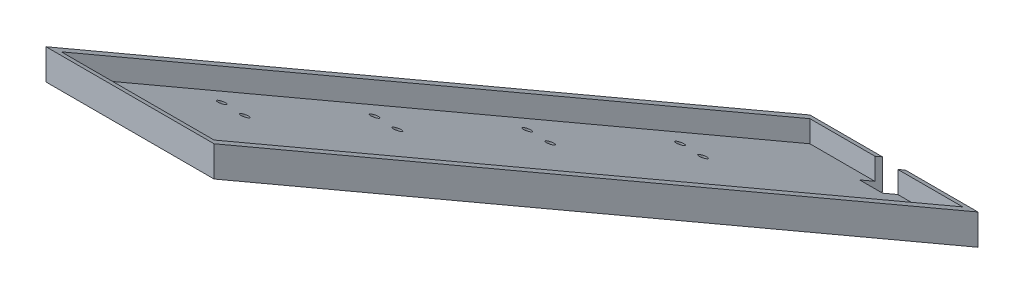
SolidWorks part; units mm, degrees
material "Acrylic (Medium-high impact)"
ref_plane "Front Plane" through (0, 0, 0) normal (0, 0, 1) x (1, 0, 0)
ref_plane "Top Plane" through (0, 0, 0) normal (0, 1, 0) x (1, 0, 0)
ref_plane "Right Plane" through (0, 0, 0) normal (1, 0, 0) x (0, 0, -1)
sketch "Sketch1" plane through (0, 0, 0) normal (1, 0, 0) x (0, 0, -1)
  line L0 (0, 20) -> (-500, 308.6751)
  line L1 (0, 20) -> (0, 0)
  line L2 (0, 0) -> (-500, 288.6751)
  line L3 (-500, 288.6751) -> (-500, 308.6751)
  line L4 (-93.7881, 0) -> (93.7881, 0) construction
  dimension "D1" = 500
  dimension "D2" = 20
  dimension "D3" = 30
extrude "Boss-Extrude1" add sketch "Sketch1" along normal blind 110
ref_plane "Plane1" through (5, 0, 0) normal (1, 0, 0) x (0, 0, -1)
sketch "Sketch3" plane through (5, 0, 0) normal (1, 0, 0) x (0, 0, -1)
  line L0 (-495, 291.5619) -> (-5, 8.6603)
  line L2 (-5, 8.6603) -> (-5, 22.8868)
  line L3 (0, 20) -> (-500, 308.6751) construction
  line L4 (-500, 288.6751) -> (0, 0) construction
  line L5 (0, 0) -> (0, 20) construction
  line L6 (-495, 291.5619) -> (-495, 305.7884)
  line L7 (-495, 305.7884) -> (-5, 22.8868)
  line L8 (-500, 308.6751) -> (-500, 288.6751) construction
  dimension "D1" = 5
  dimension "D2" = 5
  dimension "D3" = 5
extrude "Cut-Extrude1" cut sketch "Sketch3" along normal blind 100
sketch "Sketch4" plane through (0, 0, 0) normal (0, 1, 0) x (1, 0, 0)
  line L0 (110, 0) -> (0, 0) construction
  line L1 (47.5, 15) -> (62.5, 15)
  line L2 (47.5, 15) -> (47.5, -15)
  line L3 (47.5, -15) -> (62.5, -15)
  line L4 (62.5, 15) -> (62.5, -15)
  line L5 (47.5, 15) -> (62.5, -15) construction
  line L6 (47.5, -15) -> (62.5, 15) construction
  point P0 (55, 0)
  dimension "D1" = 15
  dimension "D2" = 30
extrude "Cut-Extrude2" cut sketch "Sketch4" along normal blind 90
sketch "Sketch6" plane through (0, 0, 0) normal (0, 1, 0) x (1, 0, 0)
sketch "Sketch7" plane through (0, 0, 0) normal (0, 1, 0) x (1, 0, 0)
  line L0 (20, 49.7876) -> (20, -561.1982) construction
  line L1 (90, 41.5681) -> (90, -569.4177) construction
  line L2 (55, 44.3079) -> (55, -566.6778) construction
  line L4 (5, -5) -> (5, -495) construction
  line L7 (105, -495) -> (105, -5) construction
  line L8 (-60.0832, -105) -> (204.1417, -105) construction
  line L9 (47.5, -5) -> (5, -5) construction
  circle A0 centre (20, -105) radius 2.5
  circle A1 centre (90, -105) radius 2.5
  circle A2 centre (20, -205) radius 2.5
  circle A3 centre (20, -305) radius 2.5
  circle A4 centre (20, -405) radius 2.5
  circle A5 centre (35, -205) radius 2.5
  circle A6 centre (35, -305) radius 2.5
  circle A7 centre (35, -405) radius 2.5
  circle A8 centre (35, -105) radius 2.5
  circle A9 centre (90, -205) radius 2.5
  circle A10 centre (90, -305) radius 2.5
  circle A11 centre (90, -405) radius 2.5
  circle A12 centre (75, -205) radius 2.5
  circle A13 centre (75, -305) radius 2.5
  circle A14 centre (75, -405) radius 2.5
  circle A15 centre (75, -105) radius 2.5
  dimension "D5" = 5
  dimension "D1" = 50
  dimension "D2" = 15
  dimension "D3" = 15
  dimension "D4" = 100
  dimension "D6" = 4
  dimension "D7" = 2
  dimension "D8" = 4
  dimension "D9" = 2
extrude "Cut-Extrude3" cut sketch "Sketch7" along normal blind 413
